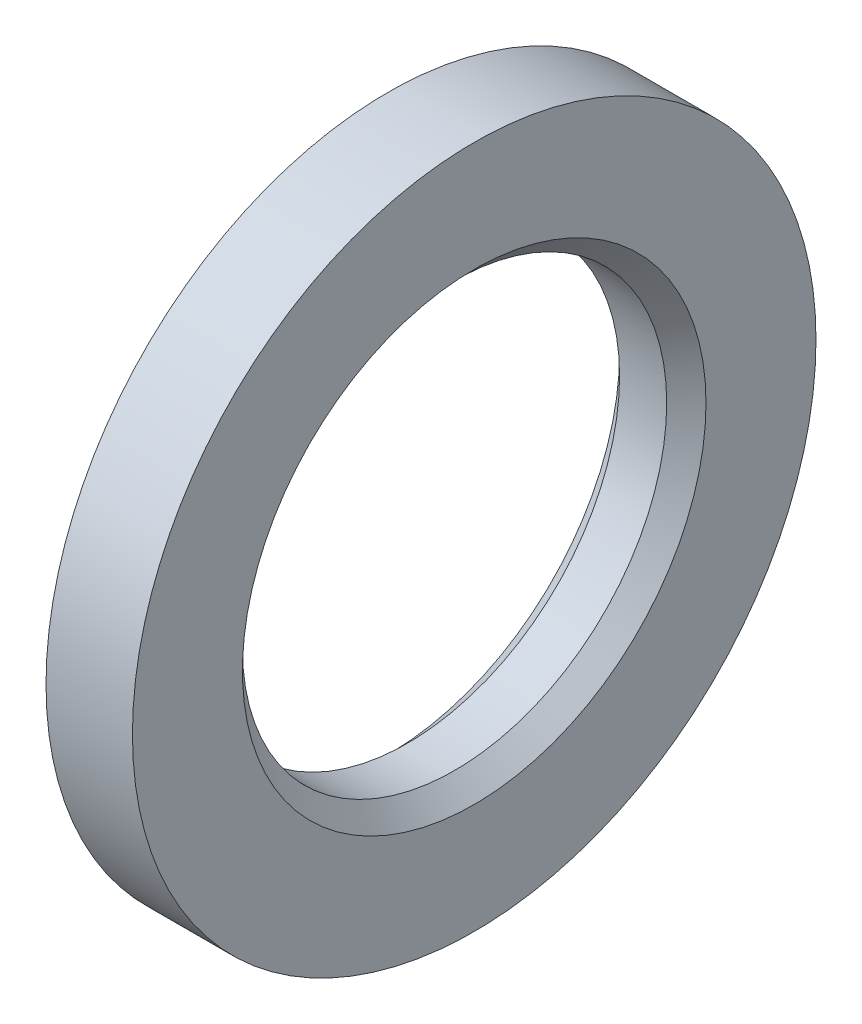
SolidWorks part; units mm, degrees
ref_plane "Front" through (0, 0, 0) normal (0, 0, 1) x (1, 0, 0)
ref_plane "Top" through (0, 0, 0) normal (0, 1, 0) x (1, 0, 0)
ref_plane "Right" through (0, 0, 0) normal (1, 0, 0) x (0, 0, -1)
sketch "Sketch1" plane through (0, 0, 0) normal (0, 0, 1) x (1, 0, 0)
  line L0 (0, 0.7493) -> (0, 1.1049)
  line L1 (0, 1.1049) -> (-0.2794, 1.1049)
  line L2 (-0.2794, 1.1049) -> (-0.2794, 0.7493)
  line L3 (-0.2794, 0.7493) -> (-0.2159, 0.6858)
  line L4 (-0.2159, 0.6858) -> (-0.0635, 0.6858)
  line L5 (-0.0635, 0.6858) -> (0, 0.7493)
  line L6 (-0.2794, 0) -> (0, 0) construction
  dimension "D1" = 0.0635
  dimension "D2" = 0.2159
  dimension "D3" = 0.2794
  dimension "D4" = 0.6858
  dimension "D5" = 0.7493
  dimension "D6" = 1.1049
revolve "Revolve1" add sketch "Sketch1" angle 360 about L6
